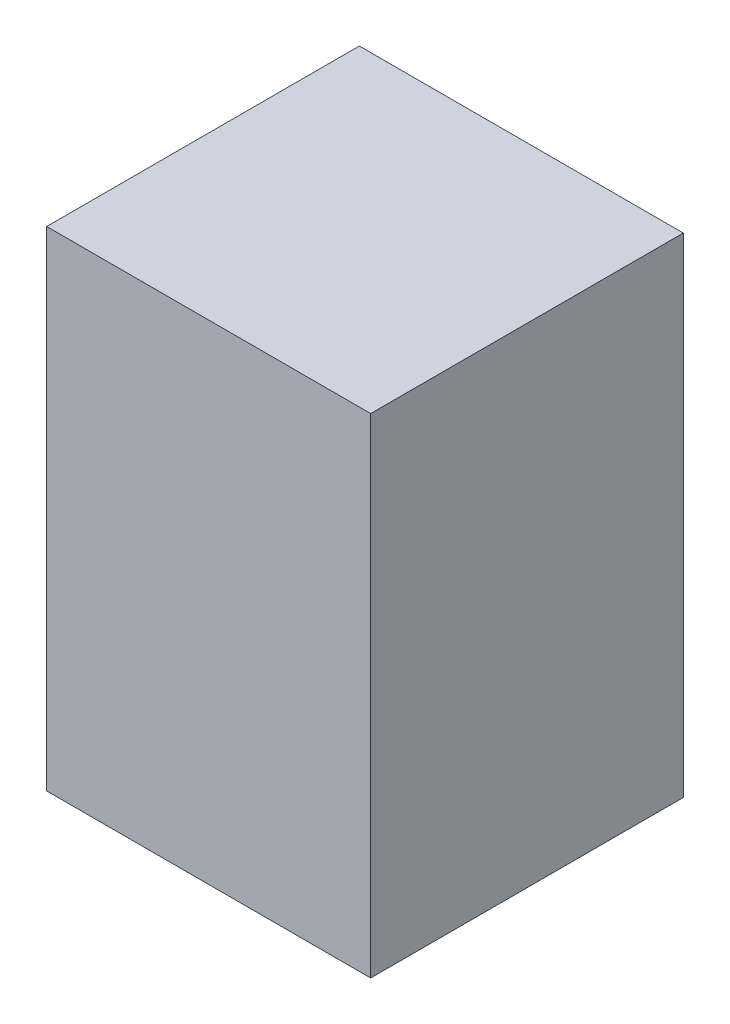
SolidWorks part; units mm, degrees
ref_plane "Front Plane" through (0, 0, 0) normal (0, 0, 1) x (1, 0, 0)
ref_plane "Top Plane" through (0, 0, 0) normal (0, 1, 0) x (1, 0, 0)
ref_plane "Right Plane" through (0, 0, 0) normal (1, 0, 0) x (0, 0, -1)
sketch "Sketch1" plane through (0, 0, 0) normal (0, 0, 1) x (1, 0, 0)
  line L0 (0, 0) -> (0, 86)
  line L1 (0, 86) -> (57, 86)
  line L2 (57, 86) -> (57, 0)
  line L3 (57, 0) -> (0, 0)
extrude "Boss-Extrude1" add sketch "Sketch1" along normal blind 55
sketch "Sketch7" plane through (0, 0, 0) normal (0, 0, -1) x (-1, 0, 0)
  circle A0 centre (-4, 1.5) radius 0.5
  circle A1 centre (-53, 1.5) radius 0.5
  circle A2 centre (-4, 84.5) radius 0.5
  circle A3 centre (-53, 84.5) radius 0.5
  point P0 (-4, 84.5)
  point P1 (-4, 1.5)
  point P2 (-53, 1.5)
  point P3 (-53, 84.5)
extrude "Cut-Extrude1" cut sketch "Sketch7" against normal blind 5
